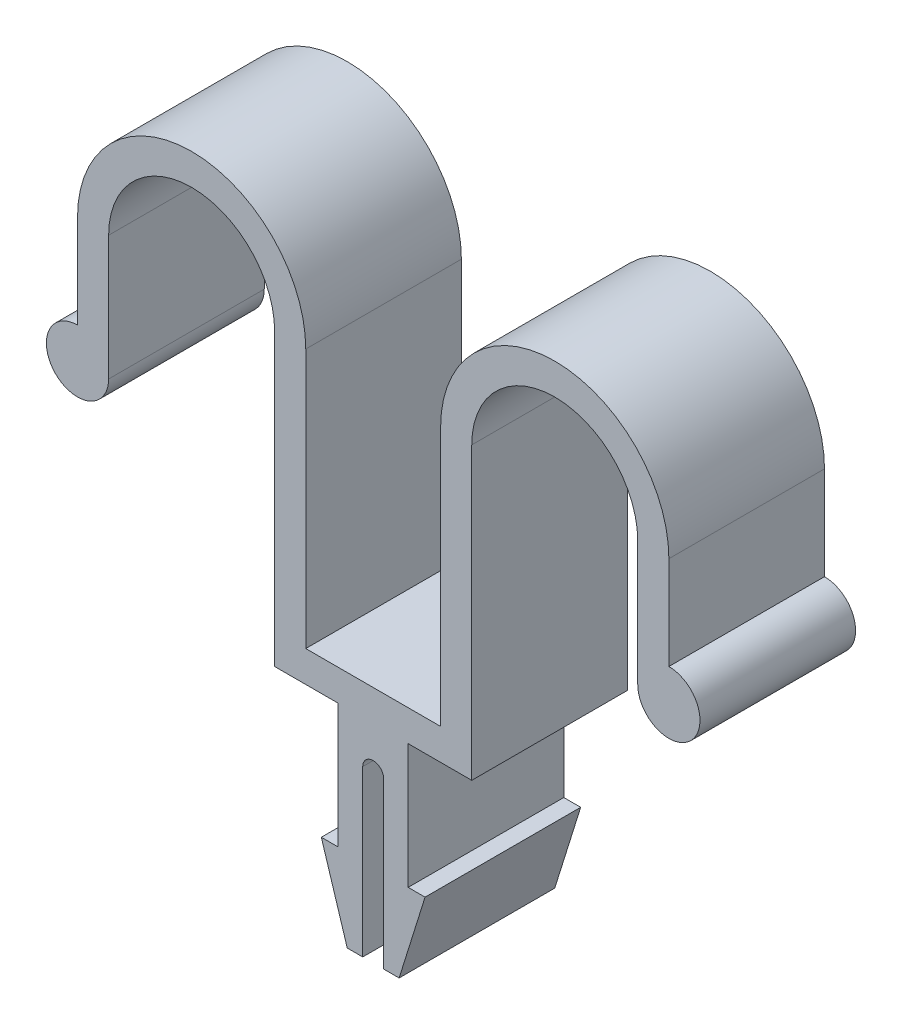
SolidWorks part; units mm, degrees
ref_plane "Ön Düzlem" through (0, 0, 0) normal (0, 0, 1) x (1, 0, 0)
ref_plane "Üst Düzlem" through (0, 0, 0) normal (0, 1, 0) x (1, 0, 0)
ref_plane "Sağ Düzlem" through (0, 0, 0) normal (1, 0, 0) x (0, 0, -1)
sketch "Sketch1" plane through (0, 0, 0) normal (0, 0, 1) x (1, 0, 0)
  line L0 (0, 3) -> (0, 12)
  line L1 (3, 0) -> (3, 12)
  line L2 (19, 12) -> (19, -16)
  line L3 (19, -16) -> (25.1286, -16)
  line L4 (25.1286, -16) -> (25.1286, -28)
  line L5 (25.1286, -28) -> (23.5, -28)
  line L6 (23.5, -28) -> (26, -36)
  line L7 (26, -36) -> (27.492, -36)
  line L8 (27.492, -36) -> (27.492, -20.1055)
  line L9 (22, 12) -> (22, -13)
  line L10 (22, -13) -> (35, -13)
  line L12 (54, 0) -> (54, 12)
  line L13 (57, 3) -> (57, 12)
  line L14 (35, 12) -> (35, -13)
  line L15 (29.508, -36) -> (29.508, -20.1055)
  line L16 (31, -36) -> (29.508, -36)
  line L17 (33.5, -28) -> (31, -36)
  line L18 (31.8714, -28) -> (33.5, -28)
  line L19 (31.8714, -16) -> (31.8714, -28)
  line L20 (38, -16) -> (31.8714, -16)
  line L21 (38, 12) -> (38, -16)
  arc A0 (0, 3) -> (3, 0) centre (0, 0) ccw
  arc A1 (3, 12) -> (19, 12) centre (11, 12) cw
  arc A2 (0, 12) -> (22, 12) centre (11, 12) cw
  arc A3 (27.492, -20.1055) -> (28.5, -19.1056) centre (28.492, -20.1055) cw
  arc A4 (57, 3) -> (54, 0) centre (57, 0) cw
  arc A5 (57, 12) -> (35, 12) centre (46, 12) ccw
  arc A6 (54, 12) -> (38, 12) centre (46, 12) ccw
  arc A7 (29.508, -20.1055) -> (28.5, -19.1056) centre (28.508, -20.1055) ccw
  point P34 (28.5, -13)
  dimension "D1" = 3
  dimension "D3" = 8
  dimension "D4" = 11
  dimension "D9" = 1
  dimension "D2" = 12
  dimension "D5" = 20
  dimension "D6" = 8
  dimension "D7" = 5
  dimension "D8" = 10
  dimension "D10" = 3
  dimension "D11" = 3
  dimension "D12" = 35
extrude "Boss-Extrude1" add sketch "Sketch1" along normal blind 15
